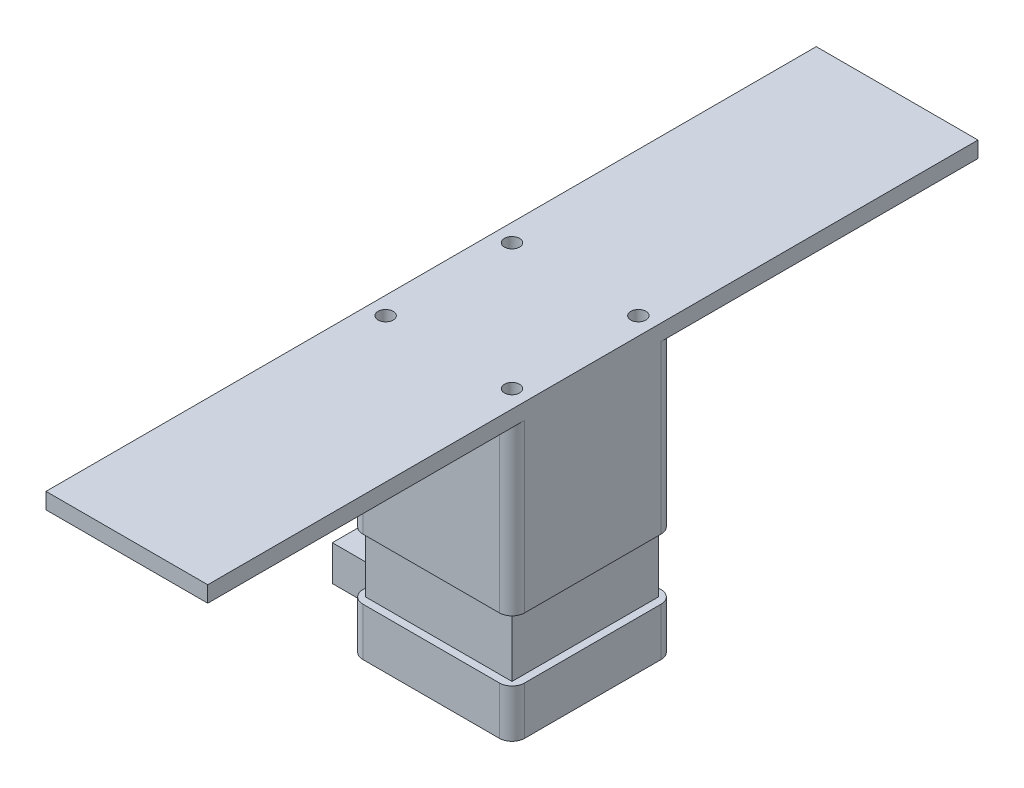
SolidWorks part; units mm, degrees
ref_plane "Front Plane" through (0, 0, 0) normal (0, 0, 1) x (1, 0, 0)
ref_plane "Top Plane" through (0, 0, 0) normal (0, 1, 0) x (1, 0, 0)
ref_plane "Right Plane" through (0, 0, 0) normal (1, 0, 0) x (0, 0, -1)
sketch "Sketch2" plane through (0, 0, 0) normal (0, 1, 0) x (1, 0, 0)
  line L1 (5, 0) -> (59, 0)
  line L2 (0, -5) -> (0, -59)
  line L3 (5, -64) -> (59, -64)
  line L4 (64, -5) -> (64, -59)
  arc A0 (5, 0) -> (0, -5) centre (5, -5) ccw
  arc A1 (59, 0) -> (64, -5) centre (59, -5) cw
  arc A2 (64, -59) -> (59, -64) centre (59, -59) cw
  arc A3 (0, -59) -> (5, -64) centre (5, -59) ccw
  point P7 (0, 0)
  point P10 (64, 0)
  point P13 (64, -64)
  point P16 (0, -64)
  dimension "D3" = 5
  dimension "D1" = 64
  dimension "D2" = 64
extrude "Boss-Extrude1" add sketch "Sketch2" along normal blind 19
sketch "Sketch3" plane through (0, 19, 0) normal (0, 1, 0) x (1, 0, 0)
  line L0 (59, 0) -> (5, 0) construction
  line L1 (3, -3) -> (61, -3)
  line L2 (3, -3) -> (3, -61)
  line L3 (3, -61) -> (61, -61)
  line L4 (61, -3) -> (61, -61)
  line L5 (64, -59) -> (64, -5) construction
  line L6 (5, -64) -> (59, -64) construction
  line L7 (0, -5) -> (0, -59) construction
  dimension "D1" = 3
  dimension "D2" = 3
  dimension "D3" = 3
  dimension "D4" = 3
extrude "Boss-Extrude2" add sketch "Sketch3" along normal blind 24
sketch "Sketch4" plane through (0, 43, 0) normal (0, 1, 0) x (1, 0, 0)
  line L1 (5, 0) -> (59, 0)
  line L2 (0, -5) -> (0, -58.9995)
  line L3 (5, -63.9995) -> (59, -63.9995)
  line L4 (64, -5) -> (64, -58.9995)
  arc A0 (0, -58.9995) -> (5, -63.9995) centre (5, -58.9995) ccw
  arc A1 (59, -63.9995) -> (64, -58.9995) centre (59, -58.9995) ccw
  arc A2 (64, -5) -> (59, 0) centre (59, -5) ccw
  arc A3 (5, 0) -> (0, -5) centre (5, -5) ccw
  point P7 (0, -63.9995)
  point P10 (64, -63.9995)
  point P13 (64, 0)
  point P16 (0, 0)
  dimension "D3" = 5
  dimension "D1" = 63.9995
  dimension "D2" = 64
extrude "Boss-Extrude3" add sketch "Sketch4" along normal blind 66 contours L2 A0 L3 A1 L4 A2 L1 A3
sketch "Sketch6" plane through (0, 0, 0) normal (-1, 0, 0) x (0, 0, 1)
  line L4 (5, 19) -> (5, 0) construction
  line L5 (18, 16) -> (46, 16)
  line L10 (18, 16) -> (18, 2)
  line L11 (18, 2) -> (46, 2)
  line L12 (46, 16) -> (46, 2)
  line L13 (59, 19) -> (59, 0) construction
  line L14 (5, 19) -> (59, 19) construction
  line L15 (5, 0) -> (59, 0) construction
  dimension "D1" = 13
  dimension "D2" = 13
  dimension "D3" = 3
  dimension "D4" = 2
extrude "Boss-Extrude4" add sketch "Sketch6" along normal blind 25.1
sketch "Sketch7" plane through (0, 109, 0) normal (0, 1, 0) x (1, 0, 0)
  line L0 (-25.1, -46) -> (-25.1, -18) construction
  line L1 (0, 120.4) -> (64, 120.4)
  line L2 (0, 120.4) -> (0, -184.4)
  line L3 (0, -184.4) -> (64, -184.4)
  line L4 (64, 120.4) -> (64, -184.4)
  line L5 (0, -5) -> (0, -58.9995) construction
  point P6 (-25.1, -32)
  dimension "D1" = 304.8
  dimension "D2" = 152.4
  dimension "D3" = 64
extrude "Boss-Extrude5" add sketch "Sketch7" along normal blind 6.35
sketch "Sketch8" plane through (0, 115.35, 0) normal (0, 1, 0) x (1, 0, 0)
  line L5 (5, -63.9995) -> (59, -63.9995) construction
  line L6 (57, -7) -> (7, -7)
  line L7 (57, -7) -> (57, -57)
  line L8 (57, -57) -> (7, -57)
  line L9 (7, -7) -> (7, -57)
  line L10 (57, -7) -> (7, -57) construction
  line L11 (57, -57) -> (7, -7) construction
  line L12 (61, -61) -> (61, -3) construction
  circle A0 centre (7, -7) radius 3
  circle A1 centre (57, -7) radius 3
  circle A2 centre (57, -57) radius 3
  circle A3 centre (7, -57) radius 3
  point P2 (32, -32)
  point P10 (32, -63.9995)
  point P13 (61, -32)
  dimension "D3" = 6
  dimension "D1" = 50
  dimension "D2" = 50
extrude "Cut-Extrude1" cut sketch "Sketch8" against normal blind 5 contours L6 A0 L9 | L9 A0 L6 | A1 | A2 | A3
